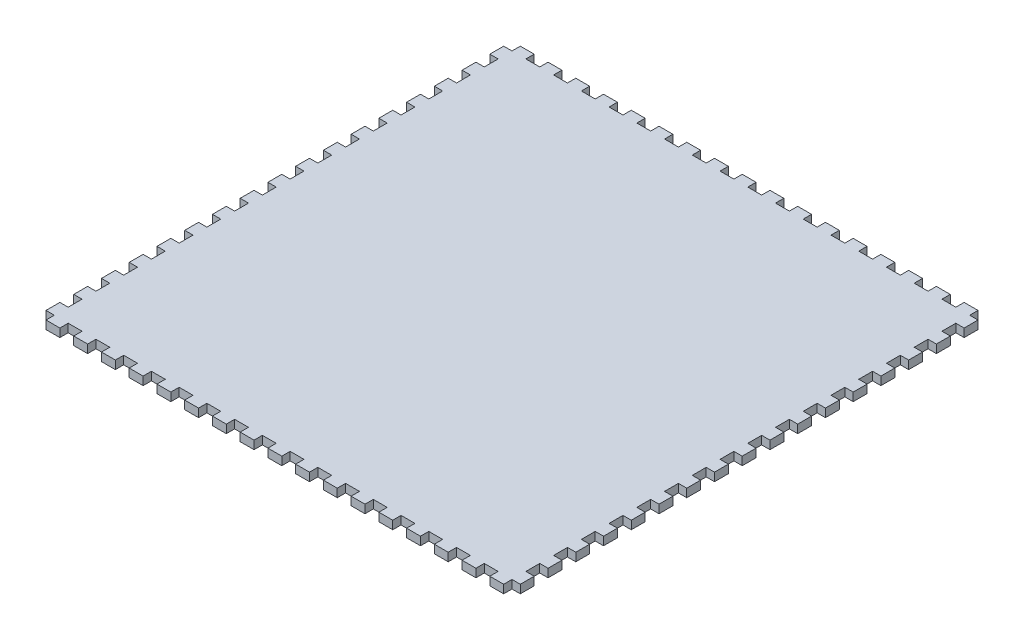
SolidWorks part; units mm, degrees
ref_plane "Спереди" through (0, 0, 0) normal (0, 0, 1) x (1, 0, 0)
ref_plane "Сверху" through (0, 0, 0) normal (0, 1, 0) x (1, 0, 0)
ref_plane "Справа" through (0, 0, 0) normal (1, 0, 0) x (0, 0, -1)
sketch "Эскиз1" plane through (0, 0, 0) normal (0, 1, 0) x (1, 0, 0)
  line L0 (0, 165) -> (0, 168)
  line L1 (5, 0) -> (10, 0)
  line L2 (0, 5) -> (0, 10)
  line L3 (5, 165) -> (10, 165)
  line L4 (165, 5) -> (165, 10)
  line L5 (0, 168) -> (5, 168)
  line L6 (5, 168) -> (5, 165)
  line L7 (10, 165) -> (10, 168)
  line L8 (10, 168) -> (15, 168)
  line L9 (15, 168) -> (15, 165)
  line L10 (20, 165) -> (20, 168)
  line L11 (20, 168) -> (25, 168)
  line L12 (25, 168) -> (25, 165)
  line L13 (30, 165) -> (30, 168)
  line L14 (30, 168) -> (35, 168)
  line L15 (35, 168) -> (35, 165)
  line L16 (40, 165) -> (40, 168)
  line L17 (40, 168) -> (45, 168)
  line L18 (45, 168) -> (45, 165)
  line L19 (50, 165) -> (50, 168)
  line L20 (50, 168) -> (55, 168)
  line L21 (55, 168) -> (55, 165)
  line L22 (60, 165) -> (60, 168)
  line L23 (60, 168) -> (65, 168)
  line L24 (65, 168) -> (65, 165)
  line L25 (70, 165) -> (70, 168)
  line L26 (70, 168) -> (75, 168)
  line L27 (75, 168) -> (75, 165)
  line L28 (80, 165) -> (80, 168)
  line L29 (80, 168) -> (85, 168)
  line L30 (85, 168) -> (85, 165)
  line L31 (90, 165) -> (90, 168)
  line L32 (90, 168) -> (95, 168)
  line L33 (95, 168) -> (95, 165)
  line L34 (100, 165) -> (100, 168)
  line L35 (100, 168) -> (105, 168)
  line L36 (105, 168) -> (105, 165)
  line L37 (110, 165) -> (110, 168)
  line L38 (110, 168) -> (115, 168)
  line L39 (115, 168) -> (115, 165)
  line L40 (120, 165) -> (120, 168)
  line L41 (120, 168) -> (125, 168)
  line L42 (125, 168) -> (125, 165)
  line L43 (130, 165) -> (130, 168)
  line L44 (130, 168) -> (135, 168)
  line L45 (135, 168) -> (135, 165)
  line L46 (140, 165) -> (140, 168)
  line L47 (140, 168) -> (145, 168)
  line L48 (145, 168) -> (145, 165)
  line L49 (150, 165) -> (150, 168)
  line L50 (150, 168) -> (155, 168)
  line L51 (155, 168) -> (155, 165)
  line L52 (160, 165) -> (160, 168)
  line L53 (160, 168) -> (165, 168)
  line L54 (165, 168) -> (165, 165)
  line L55 (15, 165) -> (20, 165)
  line L56 (25, 165) -> (30, 165)
  line L57 (35, 165) -> (40, 165)
  line L58 (45, 165) -> (50, 165)
  line L59 (55, 165) -> (60, 165)
  line L60 (65, 165) -> (70, 165)
  line L61 (75, 165) -> (80, 165)
  line L62 (85, 165) -> (90, 165)
  line L63 (95, 165) -> (100, 165)
  line L64 (105, 165) -> (110, 165)
  line L65 (115, 165) -> (120, 165)
  line L66 (125, 165) -> (130, 165)
  line L67 (135, 165) -> (140, 165)
  line L68 (145, 165) -> (150, 165)
  line L69 (155, 165) -> (160, 165)
  line L70 (0, 82.5) -> (165, 82.5) construction
  line L71 (155, 0) -> (160, 0)
  line L72 (145, 0) -> (150, 0)
  line L73 (135, 0) -> (140, 0)
  line L74 (125, 0) -> (130, 0)
  line L75 (115, 0) -> (120, 0)
  line L76 (105, 0) -> (110, 0)
  line L77 (95, 0) -> (100, 0)
  line L78 (85, 0) -> (90, 0)
  line L79 (75, 0) -> (80, 0)
  line L80 (65, 0) -> (70, 0)
  line L81 (55, 0) -> (60, 0)
  line L82 (45, 0) -> (50, 0)
  line L83 (35, 0) -> (40, 0)
  line L84 (25, 0) -> (30, 0)
  line L85 (15, 0) -> (20, 0)
  line L86 (165, -3) -> (165, 0)
  line L87 (160, -3) -> (165, -3)
  line L88 (160, 0) -> (160, -3)
  line L89 (155, -3) -> (155, 0)
  line L90 (150, -3) -> (155, -3)
  line L91 (150, 0) -> (150, -3)
  line L92 (145, -3) -> (145, 0)
  line L93 (140, -3) -> (145, -3)
  line L94 (140, 0) -> (140, -3)
  line L95 (135, -3) -> (135, 0)
  line L96 (130, -3) -> (135, -3)
  line L97 (130, 0) -> (130, -3)
  line L98 (125, -3) -> (125, 0)
  line L99 (120, -3) -> (125, -3)
  line L100 (120, 0) -> (120, -3)
  line L101 (115, -3) -> (115, 0)
  line L102 (110, -3) -> (115, -3)
  line L103 (110, 0) -> (110, -3)
  line L104 (105, -3) -> (105, 0)
  line L105 (100, -3) -> (105, -3)
  line L106 (100, 0) -> (100, -3)
  line L107 (95, -3) -> (95, 0)
  line L108 (90, -3) -> (95, -3)
  line L109 (90, 0) -> (90, -3)
  line L110 (85, -3) -> (85, 0)
  line L111 (80, -3) -> (85, -3)
  line L112 (80, 0) -> (80, -3)
  line L113 (75, -3) -> (75, 0)
  line L114 (70, -3) -> (75, -3)
  line L115 (70, 0) -> (70, -3)
  line L116 (65, -3) -> (65, 0)
  line L117 (60, -3) -> (65, -3)
  line L118 (60, 0) -> (60, -3)
  line L119 (55, -3) -> (55, 0)
  line L120 (50, -3) -> (55, -3)
  line L121 (50, 0) -> (50, -3)
  line L122 (45, -3) -> (45, 0)
  line L123 (40, -3) -> (45, -3)
  line L124 (40, 0) -> (40, -3)
  line L125 (35, -3) -> (35, 0)
  line L126 (30, -3) -> (35, -3)
  line L127 (30, 0) -> (30, -3)
  line L128 (25, -3) -> (25, 0)
  line L129 (20, -3) -> (25, -3)
  line L130 (20, 0) -> (20, -3)
  line L131 (15, -3) -> (15, 0)
  line L132 (10, -3) -> (15, -3)
  line L133 (10, 0) -> (10, -3)
  line L134 (5, -3) -> (5, 0)
  line L135 (0, -3) -> (5, -3)
  line L136 (5, 0) -> (10, 0)
  line L137 (0, 0) -> (0, -3)
  line L138 (155, 0) -> (160, 0)
  line L139 (145, 0) -> (150, 0)
  line L140 (135, 0) -> (140, 0)
  line L141 (125, 0) -> (130, 0)
  line L142 (115, 0) -> (120, 0)
  line L143 (105, 0) -> (110, 0)
  line L144 (95, 0) -> (100, 0)
  line L145 (85, 0) -> (90, 0)
  line L146 (75, 0) -> (80, 0)
  line L147 (65, 0) -> (70, 0)
  line L148 (55, 0) -> (60, 0)
  line L149 (45, 0) -> (50, 0)
  line L150 (35, 0) -> (40, 0)
  line L151 (25, 0) -> (30, 0)
  line L152 (15, 0) -> (20, 0)
  line L153 (165, 165) -> (168, 165)
  line L154 (168, 165) -> (168, 160)
  line L155 (168, 160) -> (165, 160)
  line L156 (165, 155) -> (168, 155)
  line L157 (168, 155) -> (168, 150)
  line L158 (168, 150) -> (165, 150)
  line L159 (165, 145) -> (168, 145)
  line L160 (168, 145) -> (168, 140)
  line L161 (168, 140) -> (165, 140)
  line L162 (165, 135) -> (168, 135)
  line L163 (168, 135) -> (168, 130)
  line L164 (168, 130) -> (165, 130)
  line L165 (165, 125) -> (168, 125)
  line L166 (168, 125) -> (168, 120)
  line L167 (168, 120) -> (165, 120)
  line L168 (165, 115) -> (168, 115)
  line L169 (168, 115) -> (168, 110)
  line L170 (168, 110) -> (165, 110)
  line L171 (165, 105) -> (168, 105)
  line L172 (168, 105) -> (168, 100)
  line L173 (168, 100) -> (165, 100)
  line L174 (165, 95) -> (168, 95)
  line L175 (168, 95) -> (168, 90)
  line L176 (168, 90) -> (165, 90)
  line L177 (165, 85) -> (168, 85)
  line L178 (168, 85) -> (168, 80)
  line L179 (168, 80) -> (165, 80)
  line L180 (165, 75) -> (168, 75)
  line L181 (168, 75) -> (168, 70)
  line L182 (168, 70) -> (165, 70)
  line L183 (165, 65) -> (168, 65)
  line L184 (168, 65) -> (168, 60)
  line L185 (168, 60) -> (165, 60)
  line L186 (165, 55) -> (168, 55)
  line L187 (168, 55) -> (168, 50)
  line L188 (168, 50) -> (165, 50)
  line L189 (165, 45) -> (168, 45)
  line L190 (168, 45) -> (168, 40)
  line L191 (168, 40) -> (165, 40)
  line L192 (165, 35) -> (168, 35)
  line L193 (168, 35) -> (168, 30)
  line L194 (168, 30) -> (165, 30)
  line L195 (165, 25) -> (168, 25)
  line L196 (168, 25) -> (168, 20)
  line L197 (168, 20) -> (165, 20)
  line L198 (165, 15) -> (168, 15)
  line L199 (168, 15) -> (168, 10)
  line L200 (168, 10) -> (165, 10)
  line L201 (165, 5) -> (168, 5)
  line L202 (168, 5) -> (168, 0)
  line L203 (168, 0) -> (165, 0)
  line L204 (82.5, -3) -> (82.5, 168) construction
  line L205 (-3, 5) -> (-3, 0)
  line L206 (-3, 0) -> (0, 0)
  line L207 (0, 5) -> (-3, 5)
  line L208 (-3, 10) -> (0, 10)
  line L209 (-3, 15) -> (-3, 10)
  line L210 (0, 15) -> (-3, 15)
  line L211 (-3, 20) -> (0, 20)
  line L212 (-3, 25) -> (-3, 20)
  line L213 (0, 25) -> (-3, 25)
  line L214 (-3, 30) -> (0, 30)
  line L215 (-3, 35) -> (-3, 30)
  line L216 (0, 35) -> (-3, 35)
  line L217 (-3, 40) -> (0, 40)
  line L218 (-3, 45) -> (-3, 40)
  line L219 (0, 45) -> (-3, 45)
  line L220 (-3, 50) -> (0, 50)
  line L221 (-3, 55) -> (-3, 50)
  line L222 (0, 55) -> (-3, 55)
  line L223 (-3, 60) -> (0, 60)
  line L224 (-3, 65) -> (-3, 60)
  line L225 (0, 65) -> (-3, 65)
  line L226 (-3, 70) -> (0, 70)
  line L227 (-3, 75) -> (-3, 70)
  line L228 (0, 75) -> (-3, 75)
  line L229 (-3, 80) -> (0, 80)
  line L230 (-3, 85) -> (-3, 80)
  line L231 (0, 85) -> (-3, 85)
  line L232 (-3, 90) -> (0, 90)
  line L233 (-3, 95) -> (-3, 90)
  line L234 (0, 95) -> (-3, 95)
  line L235 (-3, 100) -> (0, 100)
  line L236 (-3, 105) -> (-3, 100)
  line L237 (0, 105) -> (-3, 105)
  line L238 (-3, 110) -> (0, 110)
  line L239 (-3, 115) -> (-3, 110)
  line L240 (0, 115) -> (-3, 115)
  line L241 (-3, 120) -> (0, 120)
  line L242 (-3, 125) -> (-3, 120)
  line L243 (0, 125) -> (-3, 125)
  line L244 (-3, 130) -> (0, 130)
  line L245 (-3, 135) -> (-3, 130)
  line L246 (0, 135) -> (-3, 135)
  line L247 (-3, 140) -> (0, 140)
  line L248 (-3, 145) -> (-3, 140)
  line L249 (0, 145) -> (-3, 145)
  line L250 (-3, 150) -> (0, 150)
  line L251 (-3, 155) -> (-3, 150)
  line L252 (0, 155) -> (-3, 155)
  line L253 (-3, 160) -> (0, 160)
  line L254 (-3, 165) -> (-3, 160)
  line L255 (0, 165) -> (-3, 165)
  line L256 (165, 155) -> (165, 160)
  line L257 (165, 145) -> (165, 150)
  line L258 (165, 135) -> (165, 140)
  line L259 (165, 125) -> (165, 130)
  line L260 (165, 115) -> (165, 120)
  line L261 (165, 105) -> (165, 110)
  line L262 (165, 95) -> (165, 100)
  line L263 (165, 85) -> (165, 90)
  line L264 (165, 75) -> (165, 80)
  line L265 (165, 65) -> (165, 70)
  line L266 (165, 55) -> (165, 60)
  line L267 (165, 45) -> (165, 50)
  line L268 (165, 35) -> (165, 40)
  line L269 (165, 25) -> (165, 30)
  line L270 (0, 15) -> (0, 20)
  line L271 (0, 25) -> (0, 30)
  line L272 (0, 35) -> (0, 40)
  line L273 (0, 45) -> (0, 50)
  line L274 (0, 55) -> (0, 60)
  line L275 (0, 65) -> (0, 70)
  line L276 (0, 75) -> (0, 80)
  line L277 (0, 155) -> (0, 160)
  line L278 (0, 145) -> (0, 150)
  line L279 (0, 135) -> (0, 140)
  line L280 (0, 125) -> (0, 130)
  line L281 (0, 115) -> (0, 120)
  line L282 (0, 105) -> (0, 110)
  line L283 (0, 95) -> (0, 100)
  line L284 (0, 85) -> (0, 90)
  line L285 (165, 15) -> (165, 20)
  point P4 (12.5, 168)
  point P73 (2.5, 168)
  dimension "D1" = 165
  dimension "D2" = 5
  dimension "D3" = 3
  dimension "D4" = 5
  dimension "D6" = 10
  dimension "D7" = 3
  dimension "D8" = 17
  dimension "D5" = 17
extrude "Бобышка-Вытянуть2" add sketch "Эскиз1" along normal blind 3 contours L198 L285 L197 L196 L195 L269 L194 L193 L192 L268 L191 L190 L189 L267 L188 L187 L186 L266 L185 L184 L183 L265 L182 L181 L180 L264 L179 L178 L177 L263 L176 L175 L174 L262 L173 L172 L171 L261 L170 L169 L168 L260 L167 L166 L165 L259 L164 L163 L162 L258 L161
